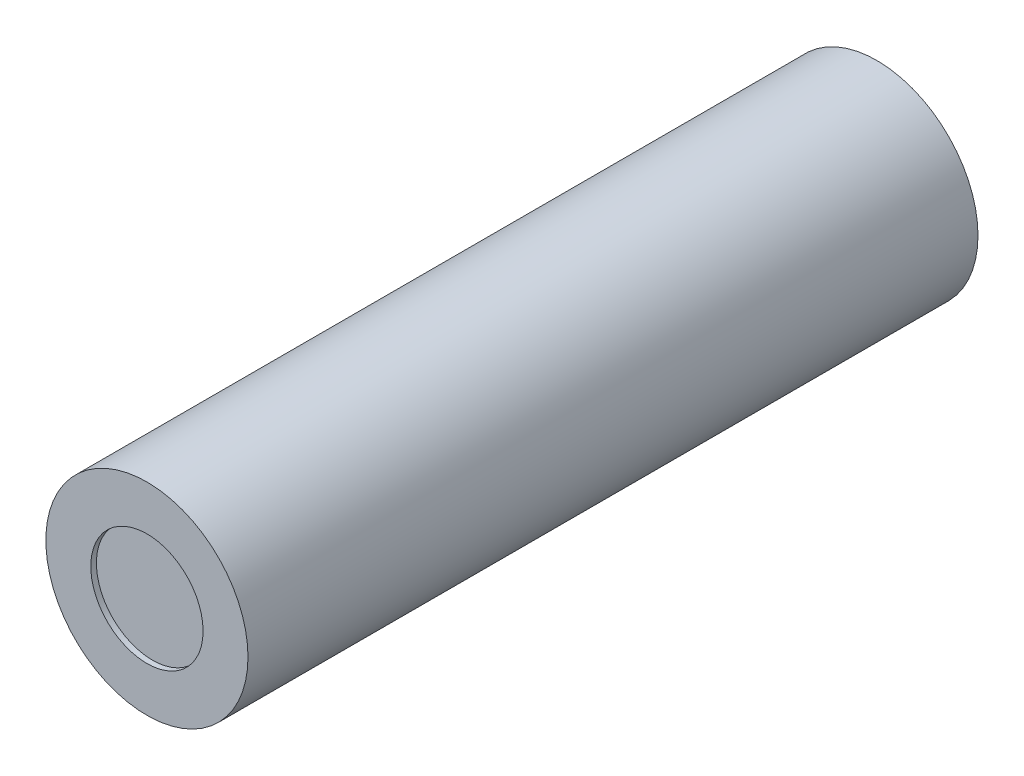
SolidWorks part; units mm, degrees
ref_plane "Front Plane" through (0, 0, 0) normal (0, 0, 1) x (1, 0, 0)
ref_plane "Top Plane" through (0, 0, 0) normal (0, 1, 0) x (1, 0, 0)
ref_plane "Right Plane" through (0, 0, 0) normal (1, 0, 0) x (0, 0, -1)
sketch "Sketch1" plane through (0, 0, 0) normal (0, 0, 1) x (1, 0, 0)
  circle A0 centre (0, 0) radius 9
extrude "Boss-Extrude1" add sketch "Sketch1" along normal blind 65
sketch "Sketch2" plane through (0, 0, 0) normal (0, 0, 1) x (1, 0, 0)
  circle A0 centre (0, 0) radius 7
extrude "Cut-Extrude1" cut sketch "Sketch2" along normal blind 0.5
ref_plane "Plane1" through (0, 0, 65) normal (0, 0, 1) x (1, 0, 0)
sketch "Sketch3" plane through (0, 0, 65) normal (0, 0, 1) x (1, 0, 0)
  circle A0 centre (0, 0) radius 5
extrude "Cut-Extrude3" cut sketch "Sketch3" against normal blind 0.5
